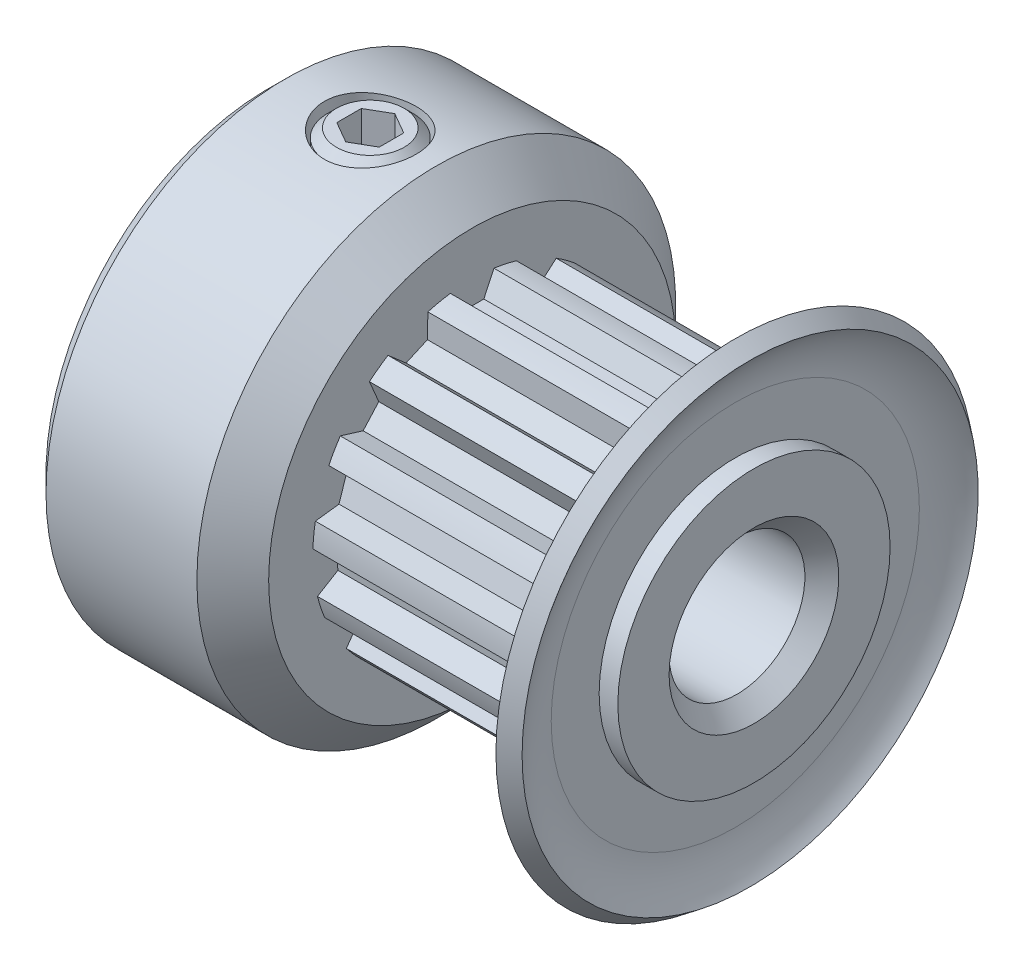
SolidWorks part; units mm, degrees
ref_plane "Front Plane" through (0, 0, 0) normal (0, 0, 1) x (1, 0, 0)
ref_plane "Top Plane" through (0, 0, 0) normal (0, 1, 0) x (1, 0, 0)
ref_plane "Right Plane" through (0, 0, 0) normal (1, 0, 0) x (0, 0, -1)
sketch "Sketch2" plane through (0, 0, 0) normal (1, 0, 0) x (0, 0, -1)
  line L3 (0, 0) -> (0, 4.0245) construction
  line L6 (0, -4.5325) -> (0, -4.85) construction
  line L7 (-0.5715, 4.4963) -> (-0.3446, 4.0097)
  line L8 (0.5715, 4.4963) -> (0.3446, 4.0097)
  line L9 (-0.5715, 4.4963) -> (-0.6418, 4.6471)
  line L10 (0.5715, 4.4963) -> (0.6418, 4.6471)
  line L12 (-0.3446, 4.0097) -> (0.3446, 4.0097)
  line L14 (0, 4.5325) -> (0, 4.85) construction
  line L15 (0, 0) -> (0, -1.143) construction
  circle A0 centre (0, 0) radius 4.85 construction
  circle A1 centre (0, 0) radius 4.0245 construction
  circle A2 centre (0, 0) radius 4.5325 construction
  arc A7 (0.6418, 4.6471) -> (-0.6418, 4.6471) centre (0, 0) ccw
  point P5 (0, 4.6912)
  dimension "D3" = 0.3175
  dimension "D1" = 50
sketch "Sketch1" plane through (0, 0, 0) normal (0, 0, 1) x (1, 0, 0)
  line L0 (-7.15, 0) -> (7.15, 0) construction
  line L1 (-7.15, 2) -> (7.15, 2)
  line L2 (-7.15, 2) -> (-7.15, 7.05)
  line L3 (-7.15, 7.05) -> (-2.207, 7.05)
  line L4 (-2.207, 7.05) -> (-1.15, 5.993)
  line L5 (-1.15, 5.993) -> (-1.15, 4.85)
  line L6 (-1.15, 4.85) -> (6.05, 4.85)
  line L7 (6.05, 4.85) -> (6.05, 5.4215)
  line L8 (6.05, 4.85) -> (7.15, 4.85) construction
  line L9 (6.6, 7.05) -> (7.15, 7.05)
  line L10 (7.15, 7.05) -> (7.15, 2)
  line L11 (6.6, 4.85) -> (6.6, 7.05) construction
  line L12 (-4.6785, 7.05) -> (-4.6785, 2) construction
  arc A0 (6.05, 5.4215) -> (6.6, 7.05) centre (8.7359, 5.4215) cw
  dimension "Bore Size" = 4
  dimension "Overall Width" = 14.3
  dimension "Inside Width" = 7.2
  dimension "Outside Width" = 8.3
  dimension "Hub Dia" = 14.1
  dimension "OD" = 14.1
  dimension "D1" = 45
  dimension "D2" = 9.7
  dimension "D3" = 1.143
  dimension "D4" = 0.5715
revolve "Revolve1" add sketch "Sketch1" angle 360 mid plane about L0
sketch "Sketch4" plane through (-1.15, 0, 0) normal (1, 0, 0) x (0, 0, -1)
  circle A0 centre (0, 0) radius 4.6912
  circle A1 centre (0, 0) radius 4.85 construction
  circle A2 centre (0, 0) radius 4.85
extrude "Cut-Extrude2" cut sketch "Sketch4" along normal up to surface (7.2 mm away) up to face at (6.05, 0, 4.85)
sketch "Sketch3" plane through (-1.15, 0, 0) normal (1, 0, 0) x (0, 0, -1)
  line L2 (-0.5715, 4.4963) -> (-0.3446, 4.0097) construction
  line L3 (-0.3446, 4.0097) -> (0.3446, 4.0097) construction
  line L4 (0.5715, 4.4963) -> (0.3446, 4.0097) construction
  line L5 (-0.6418, 4.6471) -> (-0.3446, 4.0097)
  line L6 (-0.3446, 4.0097) -> (0.3446, 4.0097)
  line L7 (0.6418, 4.6471) -> (0.3446, 4.0097)
  arc A1 (0.6418, 4.6471) -> (-0.6418, 4.6471) centre (0, 0) ccw construction
  arc A2 (0.6418, 4.6471) -> (-0.6418, 4.6471) centre (0, 0) ccw
extrude "Cut-Extrude1" cut sketch "Sketch3" along normal up to surface (7.2 mm away)
pattern_circular "CirPattern1" count 15 over 360 about axis through (0, 0, 0) along (1, 0, 0) of "Cut-Extrude1"
sketch "Sketch5" plane through (0, 0, 0) normal (0, 1, 0) x (1, 0, 0)
  line L0 (-7.15, 7.05) -> (-7.15, -7.05) construction
  line L1 (6.05, 5.4215) -> (6.05, -5.4215) construction
  line L2 (7.15, 7.05) -> (7.15, -7.05) construction
  line L3 (-1.15, 5.993) -> (-1.15, -5.993) construction
  line L4 (6.05, 5.4215) -> (6.05, -5.4215) construction
  line L5 (-7.15, 0) -> (7.15, 0) construction
  line L6 (-7.15, 0) -> (7.15, 0) construction
  point P0 (6.05, 0)
  point P14 (6.05, 0)
  point P15 (-1.15, 0)
  dimension "D1" = 14.1
  dimension "D2" = 14.1
sketch "Sketch6" plane through (0, 0, 0) normal (0, 1, 0) x (1, 0, 0)
  line L0 (-7.15, 0) -> (-5.4, 0) construction
  line L1 (-7.15, 7.05) -> (-7.15, -7.05) construction
  line L2 (-1.15, 0) -> (-2.9, 0) construction
  line L3 (-1.15, -0.3446) -> (-1.15, 0.3446) construction
  line L4 (-5.4, 0) -> (-4.15, 0) construction
  line L5 (-4.15, 0) -> (-5.0339, -0.8839) construction
  circle A0 centre (-4.15, 0) radius 1.25 construction
  circle A1 centre (-4.15, 0) radius 1.35
  point P13 (-5.0339, -0.8839)
  dimension "D1" = 0.1
  dimension "D2" = 45
  dimension "SS Dia" = 2.5
extrude "Cut-Extrude3" cut sketch "Sketch6" along normal through all
sketch "Sketch7" plane through (0, 0, 0) normal (0, 0, 1) x (1, 0, 0)
  line L0 (-5.146, 7.05) -> (-4.15, 7.05)
  line L1 (-5.4, 6.796) -> (-5.4, 2.635)
  line L2 (-5.4, 2.635) -> (-5.146, 2.381)
  line L3 (-5.146, 2.381) -> (-4.15, 2.381)
  line L4 (-4.15, 2.381) -> (-4.15, 7.05) construction
  line L6 (-5.4, 6.796) -> (-5.146, 7.05)
  line L7 (-7.15, 7.05) -> (-2.207, 7.05) construction
  line L8 (-4.15, 7.05) -> (-4.15, 2.381)
  point P0 (-5.4, 7.05)
  point P4 (-5.4, 2.381)
  dimension "D2" = 0.381
revolve "Revolve2" add sketch "Sketch7" angle 360 mid plane about L4
sketch "Sketch8" plane through (0, 7.05, 0) normal (0, 1, 0) x (1, 0, 0)
  line L0 (-4.15, 0) -> (-5.4, 0) construction
  line L1 (-4.15, 0.7217) -> (-4.775, 0.3608)
  line L2 (-4.775, 0.3608) -> (-4.775, -0.3608)
  line L3 (-4.775, -0.3608) -> (-4.15, -0.7217)
  line L4 (-4.15, -0.7217) -> (-3.525, -0.3608)
  line L5 (-3.525, -0.3608) -> (-3.525, 0.3608)
  line L6 (-3.525, 0.3608) -> (-4.15, 0.7217)
  circle A0 centre (-4.15, 0) radius 0.625 construction
  point P13 (-4.775, 0)
extrude "Cut-Extrude4" cut sketch "Sketch8" against normal blind 1.016
pattern_circular "CirPattern2" [suppressed] count 2 over 90
pattern_circular "CirPattern3" [suppressed] count 2 over 90
chamfer "Chamfer1" distance 0.5 angle 45 3 edges at (-7.15, 0, 7.05) (-7.15, 0, 2) (7.15, 0, 2)
sketch "Sketch9" plane through (0, 0, 0) normal (0, 0, 1) x (1, 0, 0)
  line L0 (7.15, 4.0097) -> (7.15, 7.05)
  line L1 (7.15, 7.05) -> (7.15, 2) construction
  line L2 (6.6, 4.85) -> (6.6, 7.05) construction
  line L3 (6.6, 5.4215) -> (6.6, 4.0097)
  line L4 (6.6, 7.05) -> (6.8022, 7.3152)
  line L5 (6.6, 4.0097) -> (7.15, 4.0097)
  line L6 (6.6, 7.05) -> (7.0374, 6.7165)
  line L7 (6.8022, 7.3152) -> (7.15, 7.05)
  line L8 (-1.15, 4.0097) -> (7.15, 4.0097) construction
  line L9 (-7.15, 0) -> (7.15, 0) construction
  line L10 (-7.15, 0) -> (7.15, 0) construction
  arc A0 (6.6, 7.05) -> (6.05, 5.4215) centre (8.7359, 5.4215) ccw construction
  arc A3 (6.6, 5.4215) -> (7.0374, 6.7165) centre (8.7359, 5.4215) cw
revolve "Cut-Revolve1" cut sketch "Sketch9" angle 360 about L0
equation "\"D3@Sketch2\" = (\"hs@Sketch2\"-\"ht@Sketch2\")/2"
equation "\"D2@Sketch1\" = \"PD@Sketch2\""
equation "\"D3@Sketch1\" = \"hs@Sketch2\""
equation "\"D4@Sketch1\" = \"D3@Sketch1\"/2"
equation "\"D1@Sketch5\"=\"Hub Dia@Sketch1\""
equation "\"D2@Sketch5\"=\"OD@Sketch1\""
